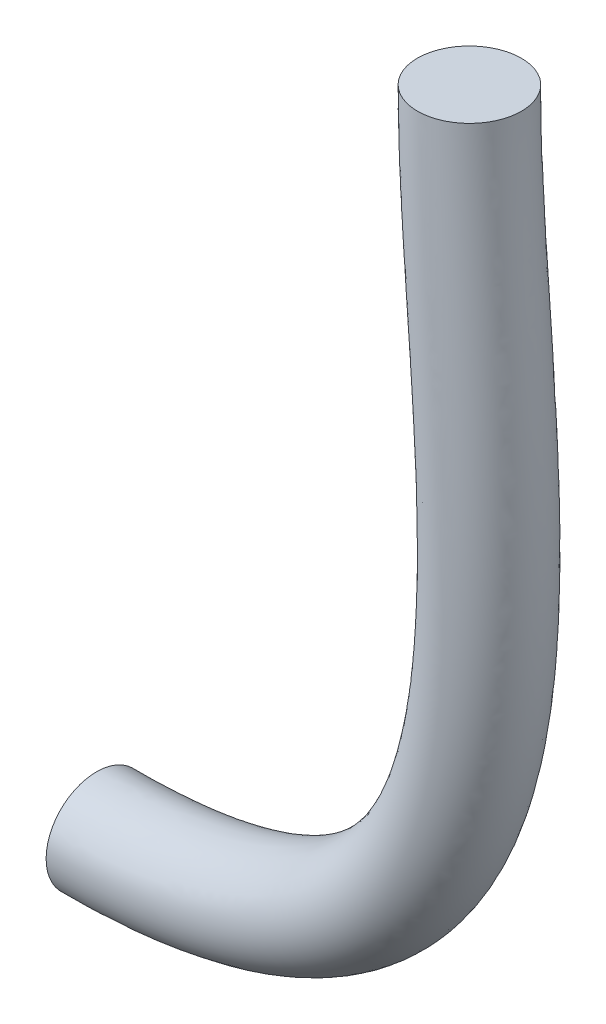
SolidWorks part; units mm, degrees
ref_plane "Płaszczyzna XY" through (0, 0, 0) normal (0, 0, 1) x (1, 0, 0)
ref_plane "Płaszczyzna XZ" through (0, 0, 0) normal (0, 1, 0) x (1, 0, 0)
ref_plane "Płaszczyzna YZ" through (0, 0, 0) normal (1, 0, 0) x (0, 0, -1)
sketch3d "Szkic 3D1"
  line L0 (-49.3095, -108.4627, -1.3267) -> (-66.3095, -108.4627, -1.3267) construction
  line L1 (-49.3095, -108.4627, -1.3267) -> (-66.3095, -108.4627, -1.3267) construction
  spline S0 degree 3 poles (0, 0, 0) (1.1837, -41.2504, 1.2485) (18.1956, -108.3227, -0.8465) (-49.3145, -108.4627, -1.3267) knots 0 0 0 0 1 1 1 1
  point P2 (1.0469, -35.8469, 0.3913)
  point P4 (1.0469, -35.8469, 0.3913)
  point P6 (1.4055, -26.6443, 0.3913)
  point P7 (0, 0, 0)
  point P9 (1.764, -23.8955, 0.3913)
  point P10 (2.003, -29.8712, 0.3913)
  point P11 (-49.3145, -108.5434, -1.37)
  point P12 (0, 0, 0)
  point P13 (-49.3095, -108.4627, -1.3267)
  point P18 (-3.6242, -84.7386, -0.3608)
ref_plane "Płaszczyzna1" through (0, 0, 0) normal (0.0287, -0.9991, 0.0302) x (-0.9996, -0.0287, 0.0007)
sketch "Szkic1" plane through (0, 0, 0) normal (0.0287, -0.9991, 0.0302) x (-0.9996, -0.0287, 0.0007)
  circle A0 centre (0, 0) radius 6.5
  dimension "D1" = 13
sweep "Wyciągnięcie po ścieżce1" add profiles "Szkic1" path "Szkic 3D1"
